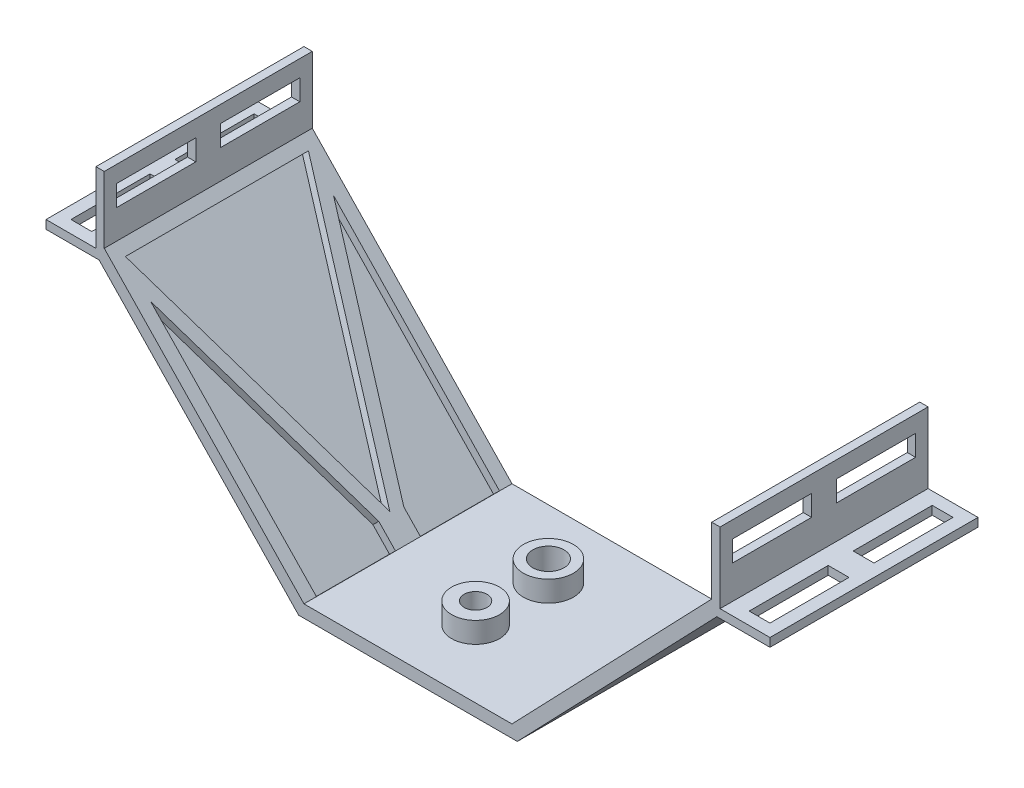
SolidWorks part; units mm, degrees
ref_plane "Front Plane" through (0, 0, 0) normal (0, 0, 1) x (1, 0, 0)
ref_plane "Top Plane" through (0, 0, 0) normal (0, 1, 0) x (1, 0, 0)
ref_plane "Right Plane" through (0, 0, 0) normal (1, 0, 0) x (0, 0, -1)
sketch "Sketch1" plane through (0, 0, 0) normal (0, 1, 0) x (1, 0, 0)
  line L0 (0, 17.5) -> (0, 0) construction
  line L2 (-25, 33.75) -> (25, 33.75)
  line L3 (-25, 33.75) -> (-25, -16.25)
  line L4 (-25, -16.25) -> (25, -16.25)
  line L5 (25, 33.75) -> (25, -16.25)
  circle A0 centre (0, 0) radius 3.75
  circle A1 centre (0, 17.5) radius 2.75
  point P9 (0, 8.75)
  dimension "D1" = 5.5
  dimension "D2" = 7.5
  dimension "D3" = 17.5
  dimension "D4" = 50
  dimension "D5" = 50
  dimension "D6" = 25
  dimension "D7" = 25
extrude "Boss-Extrude1" add sketch "Sketch1" along normal blind 3
sketch "Sketch2" plane through (0, 0, 16.25) normal (0, 0, 1) x (1, 0, 0)
  line L0 (-25, 0) -> (-26.2787, 0)
  line L1 (-26.2787, 0) -> (-74.2331, 49.9526)
  line L2 (-85, 49.9526) -> (-85, 52)
  line L3 (-85, 52) -> (-75, 52)
  line L4 (-75, 52) -> (-75, 62)
  line L5 (-75, 62) -> (-73, 62)
  line L6 (-73, 62) -> (-73, 53)
  line L7 (-73, 53) -> (-25, 3)
  line L9 (-74.2331, 49.9526) -> (-85, 49.9526)
  line L10 (-25, 3) -> (-25, 0) construction
  line L11 (-25, 3) -> (-25, 0)
  dimension "D1" = 3
  dimension "D2" = 50
  dimension "D3" = 2
  dimension "D4" = 10
  dimension "D5" = 10
extrude "Boss-Extrude2" add sketch "Sketch2" against normal blind 50
sketch "Sketch3" plane through (-11.5112, -11.0508, 0) normal (0.7214, 0.6925, 0) x (0, 0, -1)
  line L0 (8.75, 88.7884) -> (8.75, 19.4775) construction
  line L1 (33.75, 88.7884) -> (-16.25, 88.7884) construction
  line L2 (33.75, 19.4775) -> (-16.25, 19.4775) construction
  line L3 (-13.25, 85.7884) -> (30.75, 85.7884)
  line L4 (30.75, 85.7884) -> (8.75, 25.7884)
  line L5 (8.75, 25.7884) -> (-13.25, 85.7884)
  line L6 (-13.25, 85.7884) -> (-13.0633, 86.2093)
  line L7 (30.75, 77.0739) -> (11.75, 25.2557)
  line L8 (11.75, 25.2557) -> (11.75, 19.4775)
  line L9 (11.75, 19.4775) -> (30.75, 19.4775)
  line L10 (30.75, 19.4775) -> (30.75, 22.8979)
  line L11 (30.75, 77.0739) -> (30.75, 22.8979)
  line L12 (-13.25, 77.0739) -> (-13.25, 19.4775)
  line L13 (-13.25, 19.4775) -> (5.75, 19.4775)
  line L14 (5.75, 19.4775) -> (5.75, 25.2557)
  line L15 (5.75, 25.2557) -> (-13.25, 77.0739)
  line L16 (-16.25, 19.4775) -> (-16.25, 88.7884) construction
  line L17 (33.75, 19.4775) -> (33.75, 88.7884) construction
  line M2 (-16.25, 19.4775) -> (33.75, 19.4775)
  dimension "D1" = 3
  dimension "D2" = 3
  dimension "D3" = 3
  dimension "D4" = 3
  dimension "D5" = 3
  dimension "D6" = 60
  dimension "D7" = 3
  dimension "D8" = 3
  dimension "D9" = 3
extrude "Cut-Extrude2" cut sketch "Sketch3" against normal blind 2 contours L3 L0 L4 | L0 L3 L5 | L14 L15 L12 M2 | L11 L7 L8 L10 M2
ref_plane "Plane1" through (0, 0, 0) normal (1, 0, 0) x (0, 0, -1)
mirror "Mirror1" about plane through (0, 0, 0) normal (1, 0, 0) of "Cut-Extrude2", "Boss-Extrude2"
sketch "Sketch10" plane through (85, 0, 0) normal (1, 0, 0) x (0, 0, -1)
  line L1 (-16.25, 52) -> (33.75, 52)
  line L2 (-16.25, 52) -> (-16.25, 49.9526)
  line L3 (-16.25, 49.9526) -> (33.75, 49.9526)
  line L4 (33.75, 52) -> (33.75, 49.9526)
extrude "Boss-Extrude6" add sketch "Sketch10" along normal blind 2
sketch "Sketch11" plane through (0, 49.9526, 0) normal (0, -1, 0) x (-1, 0, 0)
  line L1 (-84, -13.25) -> (-79, -13.25)
  line L2 (-84, -13.25) -> (-84, 5.75)
  line L3 (-84, 30.75) -> (-79, 30.75)
  line L4 (-84, 5.75) -> (-79, 5.75)
  line L5 (-87, -16.25) -> (-74.2331, -16.25) construction
  line L6 (-87, 33.75) -> (-74.2331, 33.75) construction
  line L7 (-79, 5.75) -> (-79, -13.25)
  line L8 (-84, 11.75) -> (-84, 30.75)
  line L9 (-84, 11.75) -> (-79, 11.75)
  line L10 (-79, 11.75) -> (-79, 30.75)
  line L11 (-87, 8.75) -> (-74.2331, 8.75) construction
  line L12 (-87, -16.25) -> (-87, 33.75) construction
  line L13 (-74.2331, 33.75) -> (-74.2331, -16.25) construction
  point P8 (-80.6166, 33.75)
  dimension "D1" = 5
  dimension "D2" = 3
  dimension "D3" = 3
  dimension "D4" = 3
  dimension "D5" = 3
extrude "Cut-Extrude4" cut sketch "Sketch11" against normal blind 4
mirror "Mirror2" about plane through (0, 0, 0) normal (1, 0, 0) of "Boss-Extrude6", "Cut-Extrude4"
sketch "Sketch12" plane through (0, 62, 0) normal (0, 1, 0) x (1, 0, 0)
  line L1 (75, -16.25) -> (73, -16.25)
  line L2 (75, -16.25) -> (75, 33.75)
  line L3 (75, 33.75) -> (73, 33.75)
  line L4 (73, -16.25) -> (73, 33.75)
  line L5 (-73, -16.25) -> (-75, -16.25)
  line L6 (-73, -16.25) -> (-73, 33.75)
  line L7 (-73, 33.75) -> (-75, 33.75)
  line L8 (-75, -16.25) -> (-75, 33.75)
extrude "Boss-Extrude7" add sketch "Sketch12" along normal blind 10
sketch "Sketch13" plane through (73, 0, 0) normal (-1, 0, 0) x (0, 0, 1)
  line L0 (-33.75, 62.5) -> (16.25, 62.5) construction
  line L1 (-33.75, 53) -> (-33.75, 72) construction
  line L2 (16.25, 53) -> (16.25, 72) construction
  line L3 (-8.75, 72) -> (-8.75, 53) construction
  line L4 (-33.75, 72) -> (16.25, 72) construction
  line L5 (-33.75, 53) -> (16.25, 53) construction
  line L7 (-30.75, 65) -> (-11.75, 65)
  line L8 (-30.75, 65) -> (-30.75, 60)
  line L9 (-30.75, 60) -> (-11.75, 60)
  line L10 (-11.75, 65) -> (-11.75, 60)
  line L11 (-5.75, 65) -> (13.25, 65)
  line L12 (-5.75, 65) -> (-5.75, 60)
  line L13 (-5.75, 60) -> (13.25, 60)
  line L14 (13.25, 65) -> (13.25, 60)
  dimension "D1" = 5
  dimension "D2" = 5
  dimension "D3" = 3
  dimension "D4" = 3
  dimension "D5" = 3
  dimension "D6" = 3
  dimension "D7" = 2.5
  dimension "D8" = 2.5
extrude "Cut-Extrude5" cut sketch "Sketch13" against normal blind 10
mirror "Mirror3" about plane through (0, 0, 0) normal (1, 0, 0) of "Cut-Extrude5"
sketch "Sketch14" plane through (0, 3, 0) normal (0, 1, 0) x (1, 0, 0)
  circle A0 centre (0, 0) radius 3.75
  circle A1 centre (0, 0) radius 5.75
  circle A2 centre (0, 17.5) radius 2.75
  circle A3 centre (0, 17.5) radius 4.75
  dimension "D1" = 2
  dimension "D2" = 2
extrude "Boss-Extrude8" add sketch "Sketch14" along normal blind 5
sketch "Sketch15" plane through (73, 0, 0) normal (-1, 0, 0) x (0, 0, 1)
  line L0 (16.25, 53) -> (16.25, 72) construction
  line L1 (-33.75, 72) -> (16.25, 72)
  line L2 (-33.75, 72) -> (-33.75, 69)
  line L3 (-33.75, 69) -> (16.25, 69)
  line L4 (16.25, 72) -> (16.25, 69)
  dimension "D1" = 3
extrude "Cut-Extrude6" cut sketch "Sketch15" against normal through all both and the other way through all
sketch "Sketch16" plane through (0, 8, 0) normal (0, 1, 0) x (1, 0, 0)
  circle A0 centre (0, 0) radius 3.75
  circle A1 centre (0, 0) radius 2.75
  dimension "D1" = 5.5
extrude "Boss-Extrude9" add sketch "Sketch16" against normal up to surface (8 mm away) up to face at (0, 0, 3.75)
sketch "Sketch17" plane through (0, 8, 0) normal (0, 1, 0) x (1, 0, 0)
  circle A0 centre (0, 17.5) radius 3.75
  dimension "D1" = 7.5
extrude "Cut-Extrude7" cut sketch "Sketch17" against normal through all
sketch "Sketch18" plane through (0, 8, 0) normal (0, 1, 0) x (1, 0, 0)
  circle A0 centre (0, 17.5) radius 4.75
  circle A1 centre (0, 17.5) radius 6
  dimension "D1" = 12
extrude "Boss-Extrude10" add sketch "Sketch18" against normal up to surface (8 mm away) up to face at (0, 0, -13.75)
